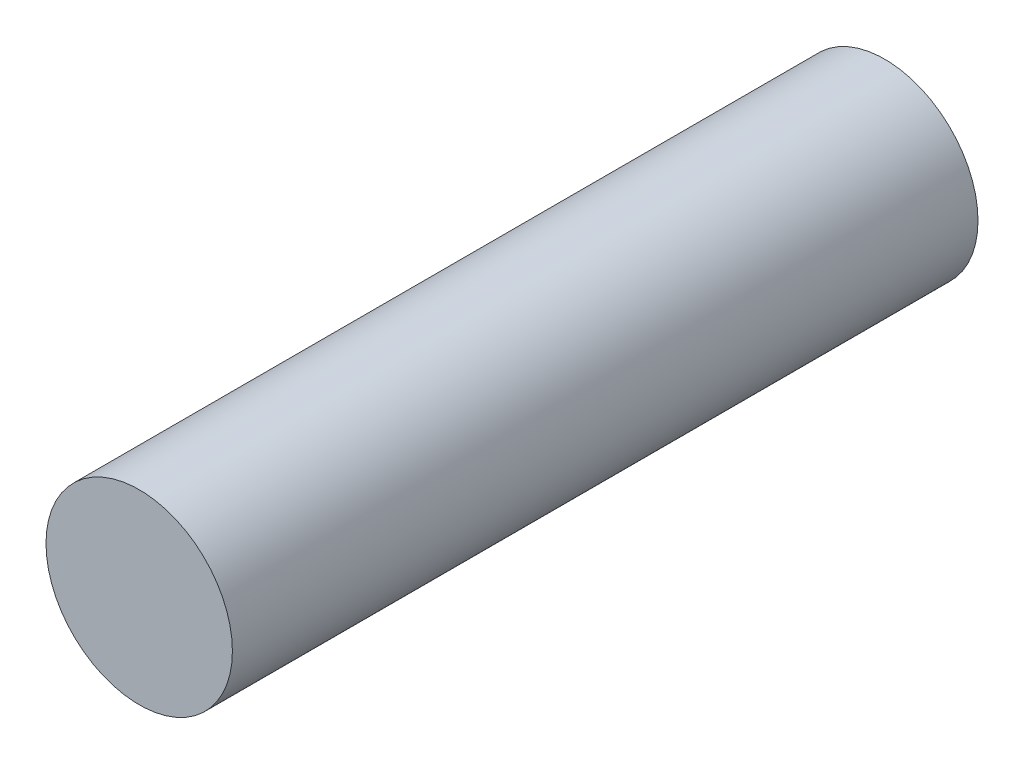
SolidWorks part; units mm, degrees
ref_plane "Front" through (0, 0, 0) normal (0, 0, 1) x (1, 0, 0)
ref_plane "Top" through (0, 0, 0) normal (0, 1, 0) x (1, 0, 0)
ref_plane "Right" through (0, 0, 0) normal (1, 0, 0) x (0, 0, -1)
sketch "Sketch1" plane through (0, 0, 0) normal (0, 0, 1) x (1, 0, 0)
  circle A0 centre (0, 0) radius 4.7625
  dimension "D1" = 9.525
extrude "Base-Extrude" add sketch "Sketch1" along normal mid plane 38.1
